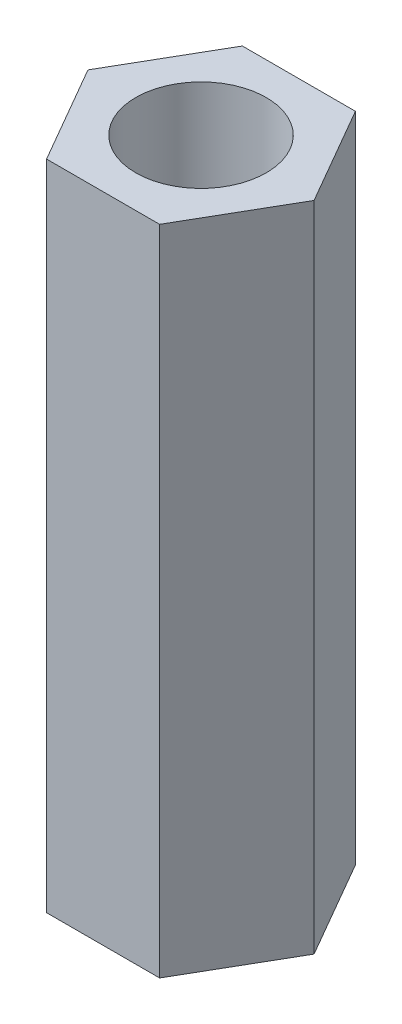
SolidWorks part; units mm, degrees
material "7075-T6 (SN)"
ref_plane "Front Plane" through (0, 0, 0) normal (0, 0, 1) x (1, 0, 0)
ref_plane "Top Plane" through (0, 0, 0) normal (0, 1, 0) x (1, 0, 0)
ref_plane "Right Plane" through (0, 0, 0) normal (1, 0, 0) x (0, 0, -1)
sketch "Sketch1" plane through (0, 0, 0) normal (0, 1, 0) x (1, 0, 0)
  line L1 (1.7321, -3) -> (3.4641, 0)
  line L2 (3.4641, 0) -> (1.7321, 3)
  line L3 (1.7321, 3) -> (-1.7321, 3)
  line L4 (-1.7321, 3) -> (-3.4641, 0)
  line L5 (-3.4641, 0) -> (-1.7321, -3)
  line L6 (-1.7321, -3) -> (1.7321, -3)
  circle A0 centre (0, 0) radius 3 construction
  circle A1 centre (0, 0) radius 2
  dimension "D1" = 4
  dimension "D2" = 6
extrude "Boss-Extrude1" add sketch "Sketch1" along normal blind 20
